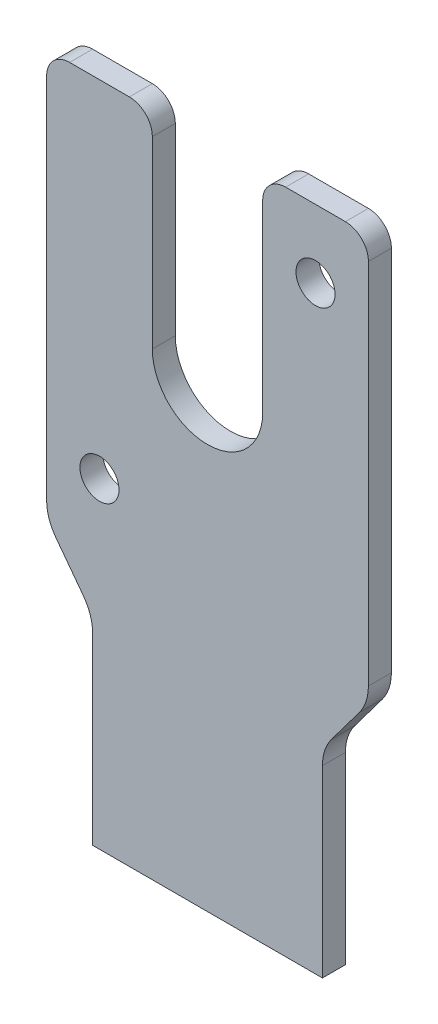
SolidWorks part; units mm, degrees
material "1.0116 (S235J2G3)"
ref_plane "Front Plane" through (0, 0, 0) normal (0, 0, 1) x (1, 0, 0)
ref_plane "Top Plane" through (0, 0, 0) normal (0, 1, 0) x (1, 0, 0)
ref_plane "Right Plane" through (0, 0, 0) normal (1, 0, 0) x (0, 0, -1)
sketch "Sketch1" plane through (0, 0, 0) normal (0, 0, 1) x (1, 0, 0)
  line L0 (0, 0) -> (0, 145) construction
  line L1 (25, 0) -> (-25, 0)
  line L2 (-35, 60) -> (-35, 140)
  line L3 (-30, 145) -> (-17, 145)
  line L4 (-12, 140) -> (-12, 100)
  line L5 (-27.4799, 64.7092) -> (33.6673, 143.2369) construction
  line L6 (-27.8953, 121.7212) -> (27.8953, 78.2788) construction
  line L7 (12, 140) -> (12, 100)
  line L8 (30, 145) -> (17, 145)
  line L10 (-25, 0) -> (-25, 40)
  line L11 (-27, 46) -> (-33, 54)
  line L12 (25, 0) -> (25, 40)
  line L13 (27, 46) -> (33, 54)
  line L14 (35, 60) -> (35, 140)
  arc A0 (-12, 100) -> (12, 100) centre (0, 100) ccw
  arc A1 (-17, 145) -> (-12, 140) centre (-17, 140) cw
  arc A2 (-35, 140) -> (-30, 145) centre (-30, 140) cw
  arc A5 (17, 145) -> (12, 140) centre (17, 140) ccw
  arc A6 (35, 140) -> (30, 145) centre (30, 140) ccw
  arc A7 (-33, 54) -> (-35, 60) centre (-25, 60) cw
  arc A8 (33, 54) -> (35, 60) centre (25, 60) ccw
  arc A9 (25, 40) -> (27, 46) centre (35, 40) cw
  arc A10 (-25, 40) -> (-27, 46) centre (-35, 40) ccw
  point P19 (0, 100)
  point P36 (-35, 56.6667)
  point P39 (35, 56.6667)
  point P42 (25, 43.3333)
  point P45 (-25, 43.3333)
  point P46 (23.5, 130.1797)
  point P47 (-23.5, 69.8203)
  point P48 (23.5, 130.1797)
  dimension "D4" = 70
  dimension "D5" = 5
  dimension "D6" = 40
  dimension "D9" = 10
  dimension "D8" = 12
  dimension "D13" = 10
  dimension "D14" = 10
  dimension "D2" = 145
  dimension "D3" = 45
  dimension "D7" = 20
  dimension "D12" = 35
extrude "Boss-Extrude1" add sketch "Sketch1" along normal blind 5
hole_wizard "Tap Drill for M10 Tap1" positions "Sketch9" profile "Sketch10" hole size "M10" standard "ISO" end condition through all
sketch "Sketch9" plane through (0, 0, 5) normal (0, 0, 1) x (1, 0, 0)
  line L0 (0, 100) -> (23.5, 130.1797) construction
  line L1 (23.5, 130.1797) -> (-25.1223, 67.7369) construction
  line L2 (-25.1223, 67.7369) -> (0, 100) construction
  point P0 (23.5, 130.1797)
  point P2 (-23.5, 69.8203)
  dimension "D1" = 23.5
  dimension "D2" = 23.5
  dimension "D3" = 76.5
sketch "Sketch10" plane through (23.5, 130.1797, 5) normal (1, 0, 0) x (0, -1, 0)
  line L0 (0, 0) -> (0, 5)
  line L1 (0, 5) -> (4.25, 5)
  line L2 (4.25, 5) -> (4.25, 0)
  line L5 (4.25, 0) -> (0, 0)
  line L11 (0, -6.35) -> (0, 107.95) construction
  dimension "Thru Hole Dia." = 8.5
  dimension "Thru Hole Depth" = 5
